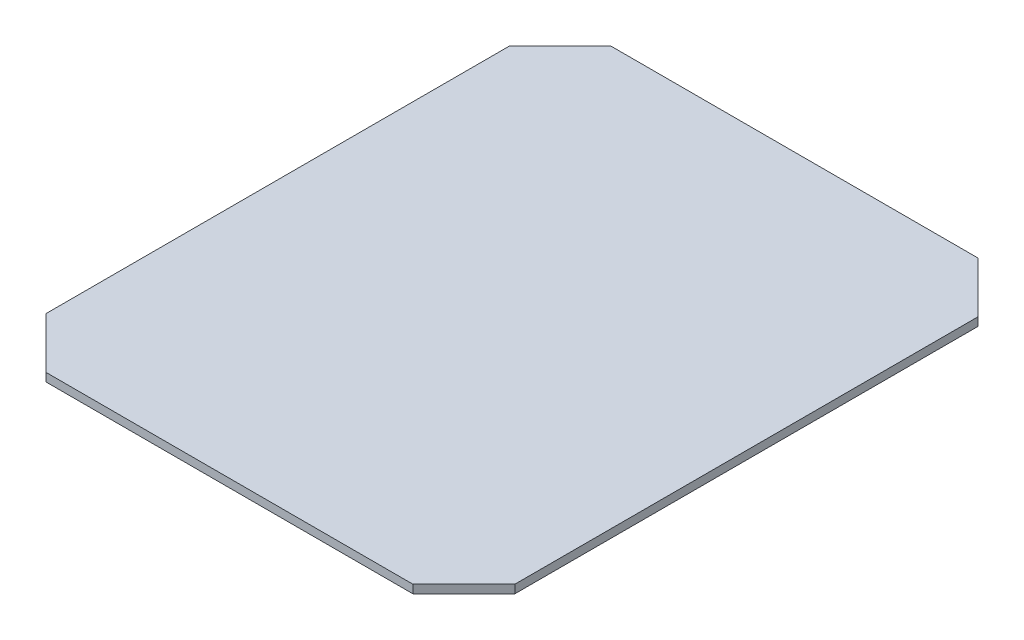
SolidWorks part; units mm, degrees
ref_plane "Front Plane" through (0, 0, 0) normal (0, 0, 1) x (1, 0, 0)
ref_plane "Top Plane" through (0, 0, 0) normal (0, 1, 0) x (1, 0, 0)
ref_plane "Right Plane" through (0, 0, 0) normal (1, 0, 0) x (0, 0, -1)
sketch "Sketch1" plane through (0, 0, 0) normal (0, 1, 0) x (1, 0, 0)
  line L1 (0, 0) -> (506.5, 0)
  line L2 (0, 0) -> (0, 610.5)
  line L3 (0, 610.5) -> (506.5, 610.5)
  line L4 (506.5, 0) -> (506.5, 610.5)
  dimension "D1" = 506.5
  dimension "D2" = 610.5
extrude "Boss-Extrude1" add sketch "Sketch1" along normal blind 9
sketch "Sketch2" plane through (0, 9, 0) normal (0, 1, 0) x (1, 0, 0)
  line L0 (0, 0) -> (55, 0)
  line L1 (0, 0) -> (506.5, 0) construction
  line L2 (55, 0) -> (0, 55)
  line L3 (0, 610.5) -> (0, 0) construction
  line L4 (0, 55) -> (0, 0)
  line L5 (506.5, 0) -> (451.5, 0)
  line L6 (451.5, 0) -> (506.5, 55)
  line L7 (506.5, 0) -> (506.5, 610.5) construction
  line L8 (506.5, 55) -> (506.5, 0)
  line L9 (506.5, 610.5) -> (506.5, 555.5)
  line L10 (506.5, 555.5) -> (451.5, 610.5)
  line L11 (506.5, 610.5) -> (0, 610.5) construction
  line L12 (451.5, 610.5) -> (506.5, 610.5)
  line L13 (0, 610.5) -> (55, 610.5)
  line L14 (55, 610.5) -> (0, 555.5)
  line L15 (0, 555.5) -> (0, 610.5)
  dimension "D1" = 55
  dimension "D2" = 55
extrude "Cut-Extrude1" cut sketch "Sketch2" against normal through all
